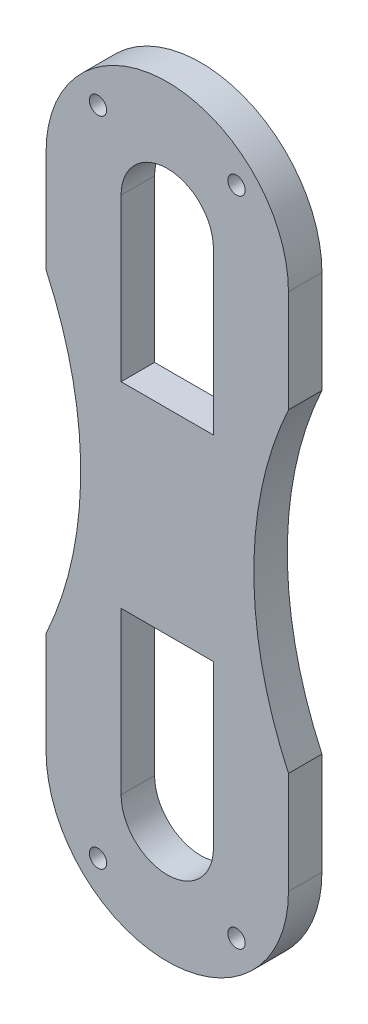
SolidWorks part; units mm, degrees
material "普通碳钢"
ref_plane "前视基准面" through (0, 0, 0) normal (0, 0, 1) x (1, 0, 0)
ref_plane "上视基准面" through (0, 0, 0) normal (0, 1, 0) x (1, 0, 0)
ref_plane "右视基准面" through (0, 0, 0) normal (1, 0, 0) x (0, 0, -1)
sketch "草图1" plane through (0, 0, 0) normal (0, 0, 1) x (1, 0, 0)
  line L0 (0, 0) -> (0, 22.5) construction
  line L1 (10.5, -13.6382) -> (10.5, -22.5)
  line L2 (-10.5, 22.5) -> (-10.5, 13.6382)
  line L3 (-4, -22.5) -> (-4, -8.5)
  line L4 (10.5, 22.5) -> (10.5, 13.6382)
  line L5 (-10.5, -13.6382) -> (-10.5, -22.5)
  line L6 (4, -22.5) -> (4, -8.5)
  line L7 (0, 0) -> (40, 0) construction
  line L8 (-4, 22.5) -> (-4, 8.5)
  line L9 (-4, 8.5) -> (4, 8.5)
  line L10 (4, 22.5) -> (4, 8.5)
  line L11 (-4, -8.5) -> (4, -8.5)
  arc A0 (10.5, 22.5) -> (-10.5, 22.5) centre (0, 22.5) ccw
  arc A1 (10.5, -22.5) -> (-10.5, -22.5) centre (0, -22.5) cw
  arc A2 (10.5, 13.6382) -> (10.5, -13.6382) centre (40, 0) ccw
  arc A3 (-10.5, 13.6382) -> (-10.5, -13.6382) centre (-40, 0) cw
  arc A4 (4, 22.5) -> (-4, 22.5) centre (0, 22.5) ccw
  arc A5 (4, -22.5) -> (-4, -22.5) centre (0, -22.5) cw
  circle A6 centre (0, 10) radius 0.75
  circle A7 centre (0, -10) radius 0.75
  circle A8 centre (-6, 28.25) radius 0.75
  circle A9 centre (6, 28.25) radius 0.75
  circle A10 centre (6, -28.25) radius 0.75
  circle A11 centre (-6, -28.25) radius 0.75
  point P0 (0, 0)
  point P15 (0, 26.5)
  point P16 (0, 19.246)
  point P21 (-4, 15.5)
  point P22 (4, 15.5)
  dimension "D3" = 21
  dimension "D2" = 65
  dimension "D6" = 8
  dimension "D9" = 1.5
  dimension "D11" = 1.5
  dimension "D1" = 21
  dimension "D4" = 45
  dimension "D5" = 40
  dimension "D7" = 8
  dimension "D8" = 18
  dimension "D10" = 20
  dimension "D12" = 12
  dimension "D13" = 56.5
extrude "凸台-拉伸1" add sketch "草图1" along normal blind 2.9 contours L2 A3 L5 A1 L1 A2 L4 A0 A9 A8 A4 L10 L9 L8 L6 A5 L3 L11 A10 A11
sketch "草图2" plane through (0, 0, 0) normal (0, 0, -1) x (-1, 0, 0)
  line L0 (4, 24.5) -> (4, 20.5)
  line L1 (0, 22.5) -> (0, 24.5) construction
  line L2 (4, 22.5) -> (4, 8.5) construction
  line L3 (4, 20.5) -> (-4, 20.5)
  line L4 (-4, 22.5) -> (-4, 8.5) construction
  line L5 (-4, 20.5) -> (-4, 24.5)
  line L6 (0, 0) -> (19.7984, 0) construction
  line L7 (4, -24.5) -> (4, -20.5)
  line L8 (-4, -20.5) -> (-4, -24.5)
  line L9 (4, -20.5) -> (-4, -20.5)
  arc A0 (4, 24.5) -> (-4, 24.5) centre (0, 24.5) ccw
  arc A1 (4, 22.5) -> (-4, 22.5) centre (0, 22.5) ccw construction
  arc A2 (4, -24.5) -> (-4, -24.5) centre (0, -24.5) cw
  dimension "D1" = 2
sketch "草图3" plane through (0, 0, 2.9) normal (0, 0, -1) x (-1, 0, 0)
  line L0 (0, 22.5) -> (28.5024, 22.5) construction
  line L1 (0, 22.5) -> (0, 10.4273) construction
  line L2 (0, -22.5) -> (29.5102, -22.5) construction
  line L3 (0, -22.5) -> (0, -39.0979) construction
  line L4 (0, 22.5) -> (-21.1451, 22.5) construction
  line L5 (0, -22.5) -> (-29.6003, -22.5) construction
sketch "草图5" plane through (0, 0, 0) normal (1, 0, 0) x (0, 0, -1)
  line L0 (-2.9, 22.5) -> (-31.5718, 22.5) construction
  line L1 (-2.9, -22.5) -> (-31.5718, -22.5) construction
